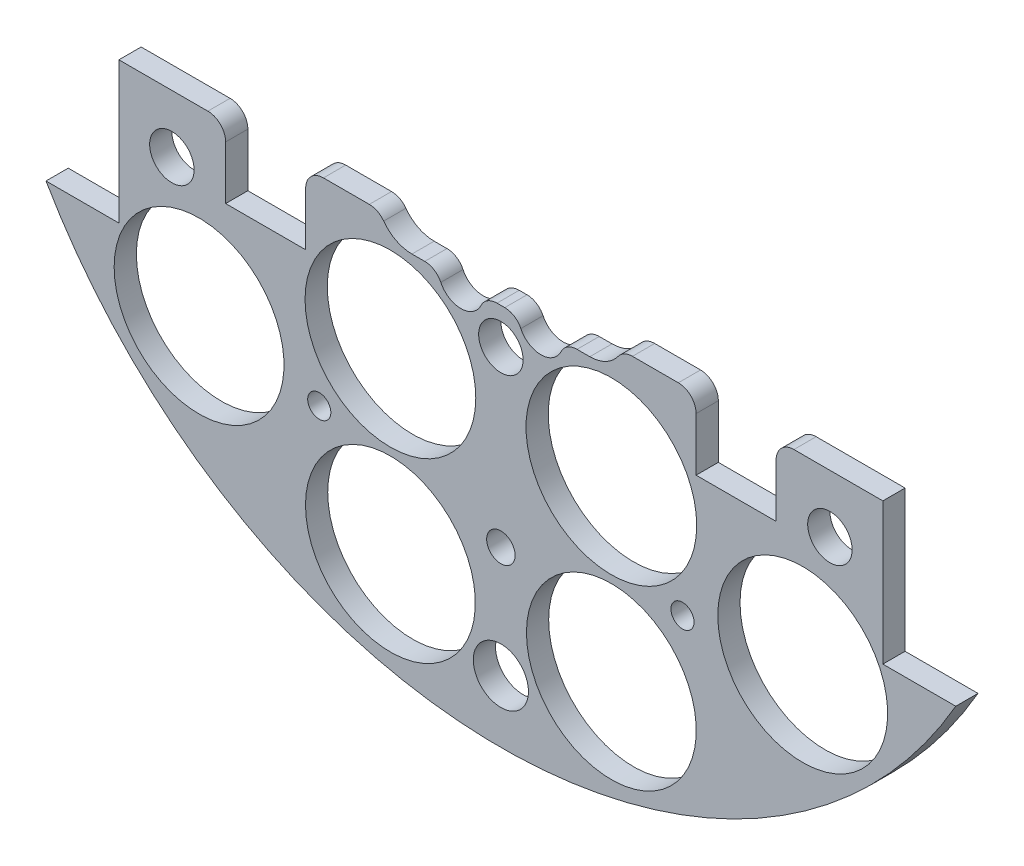
SolidWorks part; units mm, degrees
ref_plane "Front Plane" through (0, 0, 0) normal (0, 0, 1) x (1, 0, 0)
ref_plane "Top Plane" through (0, 0, 0) normal (0, 1, 0) x (1, 0, 0)
ref_plane "Right Plane" through (0, 0, 0) normal (1, 0, 0) x (0, 0, -1)
sketch "Sketch1" plane through (0, 0, 0) normal (0, 0, 1) x (1, 0, 0)
  line L0 (0, 0) -> (-82.1241, 0) construction
  line L1 (0, 0) -> (0, 95.6219) construction
  line L3 (-64.9644, 37.338) -> (-54.5504, 37.338)
  line L5 (-64.9644, -37.338) -> (-54.5504, -37.338)
  line L6 (-54.5504, 37.338) -> (-54.5504, -37.338)
  line L7 (64.9644, -37.338) -> (54.5504, -37.338)
  line L8 (64.9644, 37.338) -> (54.5504, 37.338)
  line L9 (54.5504, 37.338) -> (54.5504, -37.338)
  arc A0 (-64.9644, -37.338) -> (64.9644, -37.338) centre (0, 0) ccw
  circle A1 centre (-46.482, 11.049) radius 1.651
  circle A2 centre (-21.0833, 10.795) radius 1.651
  circle A3 centre (-21.0833, -10.795) radius 1.651
  circle A4 centre (-46.482, -11.049) radius 1.651
  circle A5 centre (46.482, -11.049) radius 1.651
  circle A6 centre (21.0833, -10.795) radius 1.651
  circle A7 centre (21.0833, 10.795) radius 1.651
  circle A8 centre (46.482, 11.049) radius 1.651
  arc A9 (64.9644, 37.338) -> (-64.9644, 37.338) centre (0, 0) ccw
  dimension "D2" = 3.302
  dimension "D3" = 3.302
  dimension "D4" = 25.4
  dimension "D5" = 10.795
  dimension "D10" = 46.482
  dimension "D6" = 74.676
  dimension "D7" = 10.414
  dimension "D8" = 74.93
  dimension "D9" = 74.93
  dimension "D11" = 37.338
extrude "Boss-Extrude2" add sketch "Sketch1" along normal blind 3.175
sketch "Sketch2" plane through (0, 0, 3.175) normal (0, 0, 1) x (1, 0, 0)
  line L0 (0, 68.58) -> (0, 55.88) construction
  line L1 (-9.525, 68.58) -> (9.525, 68.58)
  line L2 (-9.525, 68.58) -> (-9.525, 55.88)
  line L3 (-9.525, 55.88) -> (9.525, 55.88)
  line L4 (9.525, 68.58) -> (9.525, 55.88)
  line L5 (-9.525, 62.23) -> (9.525, 62.23) construction
  arc A0 (64.9644, 37.338) -> (-64.9644, 37.338) centre (0, 0) ccw construction
  circle A1 centre (-21.0833, 10.795) radius 1.651 construction
  circle A2 centre (21.0833, 10.795) radius 1.651 construction
  circle A3 centre (-6.731, 62.23) radius 1.143
  circle A4 centre (6.731, 62.23) radius 1.143
  dimension "D4" = 2.286
  dimension "D5" = 0
  dimension "D6" = 6.731
  dimension "D1" = 19.05
  dimension "D2" = 12.7
  dimension "D3" = 55.88
extrude "Cut-Extrude1" cut sketch "Sketch2" against normal through all contours A3 | A4
sketch "Sketch3" plane through (0, 0, 0) normal (0, 0, -1) x (-1, 0, 0)
  line L0 (0, 0) -> (0, -116.2908) construction
  line L1 (0, 0) -> (-153.8039, 0) construction
  line L2 (0, 0) -> (15.2681, -56.9814) construction
  line L3 (0, 0) -> (15.2302, -26.3795) construction
  circle A0 centre (-15.7776, -58.8828) radius 12.1285
  circle A3 centre (15.7776, -58.8828) radius 12.1285
  circle A4 centre (-43.1052, -43.1052) radius 12.1285
  circle A8 centre (-43.1052, 43.1052) radius 12.1285
  circle A11 centre (43.1052, 43.1052) radius 12.1285
  circle A14 centre (43.1052, -43.1052) radius 12.1285
  circle A33 centre (58.8828, -15.7776) radius 12.1285 [skipped]
  circle A34 centre (58.8828, 15.7776) radius 12.1285 [skipped]
  circle A35 centre (-58.8828, 15.7776) radius 12.1285 [skipped]
  circle A36 centre (-58.8828, -15.7776) radius 12.1285 [skipped]
  circle A37 centre (-15.7776, 58.8828) radius 12.1285 [skipped]
  circle A38 centre (15.7776, 58.8828) radius 12.1285 [skipped]
  point P36 (0, 0)
  point P53 (0, 0)
  point P55 (0, 0)
  dimension "D3" = 0
  dimension "D4" = 15
  dimension "D5" = 24.257
  dimension "D7" = 12
  dimension "D9" = 30
extrude "Cut-Extrude2" cut sketch "Sketch3" against normal through all
sketch "Sketch4" plane through (0, 0, 0) normal (0, 0, -1) x (-1, 0, 0)
  line L1 (-15.7702, 56.3138) -> (12.7925, 56.3138)
  line L2 (-15.7702, 56.3138) -> (-15.7702, 67.9913)
  line L3 (-15.7702, 67.9913) -> (12.7925, 67.9913)
  line L4 (12.7925, 56.3138) -> (12.7925, 67.9913)
extrude "Boss-Extrude3" add sketch "Sketch4" against normal up to surface (3.175 mm away) up to face at (-55.2337, -43.1052, 3.175)
sketch "Sketch5" plane through (0, 0, 0) normal (0, 0, -1) x (-1, 0, 0)
  line L1 (-85.044, -17.145) -> (131.6774, -17.145)
  line L2 (-85.044, -17.145) -> (-85.044, 113.4242)
  line L3 (-85.044, 113.4242) -> (131.6774, 113.4242)
  line L4 (131.6774, -17.145) -> (131.6774, 113.4242)
  circle A0 centre (-21.0833, -10.795) radius 1.651 construction
  dimension "D1" = 6.35
extrude "Cut-Extrude4" cut sketch "Sketch5" against normal through all contours L2 L3 L4 L1
extrude "Cut-Extrude5" cut sketch "Sketch6" against normal through all both and the other way through all
sketch "Sketch6" plane through (31.3134, 132.614, -3.175) normal (0, 0, -1) x (0, 1, 0)
  line L0 (-132.614, -31.3134) -> (-132.614, 57.8454) construction
  line L1 (-132.614, -31.3134) -> (-222.516, -31.3134) construction
  circle A0 centre (-158.014, 14.4066) radius 3.175
  circle A1 centre (-173.254, -31.3134) radius 3.175
  circle A3 centre (-158.014, -77.0334) radius 3.175
  circle A4 centre (-107.214, -77.0334) radius 3.175
  circle A5 centre (-91.974, -31.3134) radius 3.175
  circle A6 centre (-107.214, 14.4066) radius 3.175
extrude "Cut-Extrude7" cut sketch "Sketch8" against normal blind 29.21
sketch "Sketch8" plane through (31.3134, 132.559, 0) normal (0, 0, -1) x (0, 1, 0)
  line L0 (-132.559, -31.3134) -> (6.1626, -31.3134) construction
  line L2 (-132.559, -31.3134) -> (-132.559, -122.6589) construction
  circle A0 centre (-190.979, 2.9766) radius 1.651
  circle A2 centre (-154.784, -31.3134) radius 1.651
  circle A3 centre (-190.979, -65.6034) radius 1.651
  circle A4 centre (-110.334, -31.3134) radius 1.651
  circle A5 centre (-74.139, -65.6034) radius 1.651
  circle A6 centre (-74.139, 2.9766) radius 1.651
sketch "Sketch11" plane through (0, 0, 0) normal (0, 0, -1) x (-1, 0, 0)
  line L0 (-54.5504, -17.145) -> (54.5504, -17.145) construction
  circle A0 centre (0, -66.045) radius 3.937
  point P4 (0, -17.145)
  dimension "D1" = 7.874
  dimension "D2" = 48.9
extrude "Cut-Extrude11" cut sketch "Sketch11" against normal through all
sketch "Sketch12" plane through (0, 0, 0) normal (0, 0, -1) x (-1, 0, 0)
  line L0 (-54.5504, -17.145) -> (54.5504, -17.145) construction
  line L1 (-39.3104, -17.145) -> (-27.8804, -17.145)
  line L2 (-39.3104, -17.145) -> (-39.3104, -27.305)
  line L3 (-39.3104, -27.305) -> (-27.8804, -27.305)
  line L4 (-27.8804, -17.145) -> (-27.8804, -27.305)
  line L5 (-54.5504, -37.338) -> (-54.5504, -17.145) construction
  line L6 (27.8804, -17.145) -> (39.3104, -17.145)
  line L7 (27.8804, -17.145) -> (27.8804, -27.305)
  line L8 (27.8804, -27.305) -> (39.3104, -27.305)
  line L9 (39.3104, -17.145) -> (39.3104, -27.305)
  line L10 (0, -10.2409) -> (0, -88.0539) construction
  dimension "D1" = 15.24
  dimension "D2" = 11.43
  dimension "D3" = 10.16
extrude "Cut-Extrude12" cut sketch "Sketch12" against normal through all
sketch "Sketch16" plane through (0, 0, 0) normal (0, 0, -1) x (-1, 0, 0)
  line L0 (0, 0) -> (0, 27.5884) construction
  circle A0 centre (15.7776, -33.4828) radius 12.192
  circle A2 centre (15.7776, -58.8828) radius 12.1285 construction
  circle A3 centre (-15.7776, -33.4828) radius 12.192
  dimension "D1" = 24.384
  dimension "D2" = 25.4
  dimension "D3" = 0
extrude "Cut-Extrude16" cut sketch "Sketch16" against normal blind 21.59
sketch "Sketch57" plane through (0, 0, 0) normal (0, 0, -1) x (-1, 0, 0)
  line L0 (0, 0) -> (0, -110.6636) construction
  circle A0 centre (-25.9376, -45.6452) radius 1.651
  circle A1 centre (-43.1052, -43.1052) radius 12.1285 construction
  circle A2 centre (-15.7776, -33.4828) radius 12.192 construction
  circle A3 centre (25.9376, -45.6452) radius 1.651
  dimension "D1" = 3.302
  dimension "D2" = 2.54
  dimension "D3" = 10.16
extrude "Cut-Extrude57" cut sketch "Sketch57" against normal blind 58.674
extrude "Cut-Extrude58" cut sketch "Sketch58" against normal blind 48.768 and the other way blind 103.378
sketch "Sketch58" plane through (30.092, 4.0835, 36.1315) normal (0, 0, -1) x (-1, 0, 0)
  line L0 (30.092, -4.0835) -> (148.6336, -4.0835) construction
  line L1 (30.092, -4.0835) -> (30.092, 90.452) construction
  circle A0 centre (-16.898, 21.3165) radius 3.175
  circle A1 centre (77.082, 21.3165) radius 3.175
  circle A2 centre (30.092, 21.3165) radius 3.175
  circle A4 centre (77.082, -29.4835) radius 3.175
  circle A5 centre (30.092, -29.4835) radius 3.175
  circle A6 centre (-16.898, -29.4835) radius 3.175
sketch "Sketch15" plane through (0, 0, 0) normal (0, 0, -1) x (-1, 0, 0)
  line L0 (0, 0) -> (0, 42.4042) construction
  line L1 (-12.7, -20.24) -> (-8.889, -20.24)
  line L2 (-2.541, -20.24) -> (2.541, -20.24)
  line L3 (-1.06, -15.24) -> (7.7, -15.24)
  line L4 (8.889, -20.24) -> (12.7, -20.24)
  arc A0 (-9.38, -11.5013) -> (-12.7, -20.24) centre (-12.7, -15.24) ccw
  arc A1 (7.7, -15.24) -> (12.7, -20.24) centre (12.7, -15.24) cw
  arc A2 (-1.06, -15.24) -> (-9.38, -11.5013) centre (-6.06, -15.24) ccw
  arc A3 (-8.889, -20.24) -> (-2.541, -20.24) centre (-5.715, -20.32) ccw
  arc A4 (2.541, -20.24) -> (8.889, -20.24) centre (5.715, -20.32) ccw
  dimension "D1" = 10
  dimension "D4" = 6.35
  dimension "D6" = 6.35
  dimension "D2" = 15.24
  dimension "D3" = 12.7
  dimension "D5" = 6.64
  dimension "D7" = 11.43
  dimension "D8" = 5.715
  dimension "D9" = 20.32
extrude "Cut-Extrude15" cut sketch "Sketch15" against normal blind 21.59
fillet "Fillet1" radius 2.54 10 edges at (-27.8804, -17.145, 1.5875) (-39.3104, -17.145, 1.5875) (-17.3229, -17.145, 1.5875) (-8.889, -20.24, 1.5875) (-2.541, -20.24, 1.5875) (2.541, -20.24, 1.5875) (8.889, -20.24, 1.5875) (17.3229, -17.145, 1.5875) (27.8804, -17.145, 1.5875) (39.3104, -17.145, 1.5875)
sketch "Sketch59" plane through (0, 0, 0) normal (0, 0, -1) x (-1, 0, 0)
  line L0 (-25.3404, -17.145) -> (-18.7904, -17.145) construction
  circle A0 centre (0, -50.165) radius 2.032
  dimension "D1" = 4.064
  dimension "D2" = 33.02
extrude "Cut-Extrude59" cut sketch "Sketch59" against normal blind 11.938
